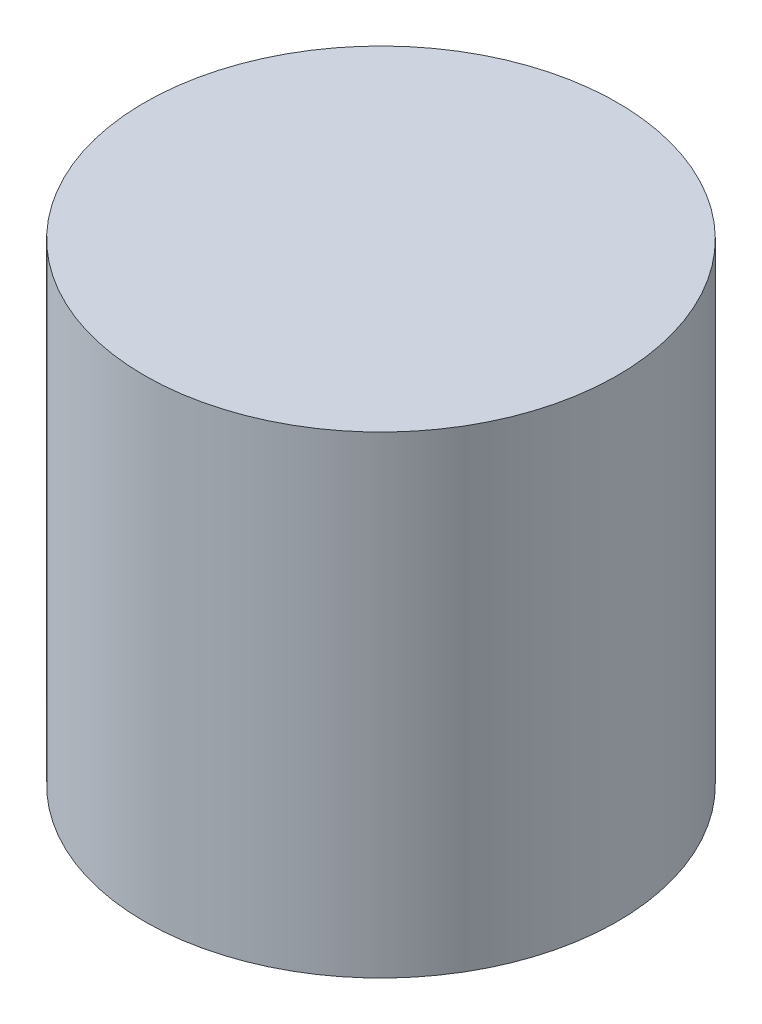
SolidWorks part; units mm, degrees
ref_plane "Front Plane" through (0, 0, 0) normal (0, 0, 1) x (1, 0, 0)
ref_plane "Top Plane" through (0, 0, 0) normal (0, 1, 0) x (1, 0, 0)
ref_plane "Right Plane" through (0, 0, 0) normal (1, 0, 0) x (0, 0, -1)
sketch "Sketch2" plane through (0, 0, 0) normal (0, 1, 0) x (1, 0, 0)
  circle A0 centre (0, 0) radius 9.525
  dimension "D1" = 19.05
extrude "Boss-Extrude1" add sketch "Sketch2" along normal blind 19.05
sketch "Sketch5" [suppressed] plane through (0, 0, 0) normal (0, -1, 0) x (1, 0, 0)
  line L0 (0, -9.525) -> (0, 9.525)
  line L1 (-9.525, 0) -> (9.525, 0)
  circle A0 centre (0, 0) radius 9.525 construction
  circle A1 centre (0, 0) radius 9.525 construction
sketch "Sketch7" plane through (0, 19.05, 0) normal (0, 1, 0) x (1, 0, 0)
  line L0 (-9.525, 0) -> (9.525, 0)
  line L1 (0, 9.525) -> (0, -9.525)
  circle A0 centre (0, 0) radius 9.525 construction
